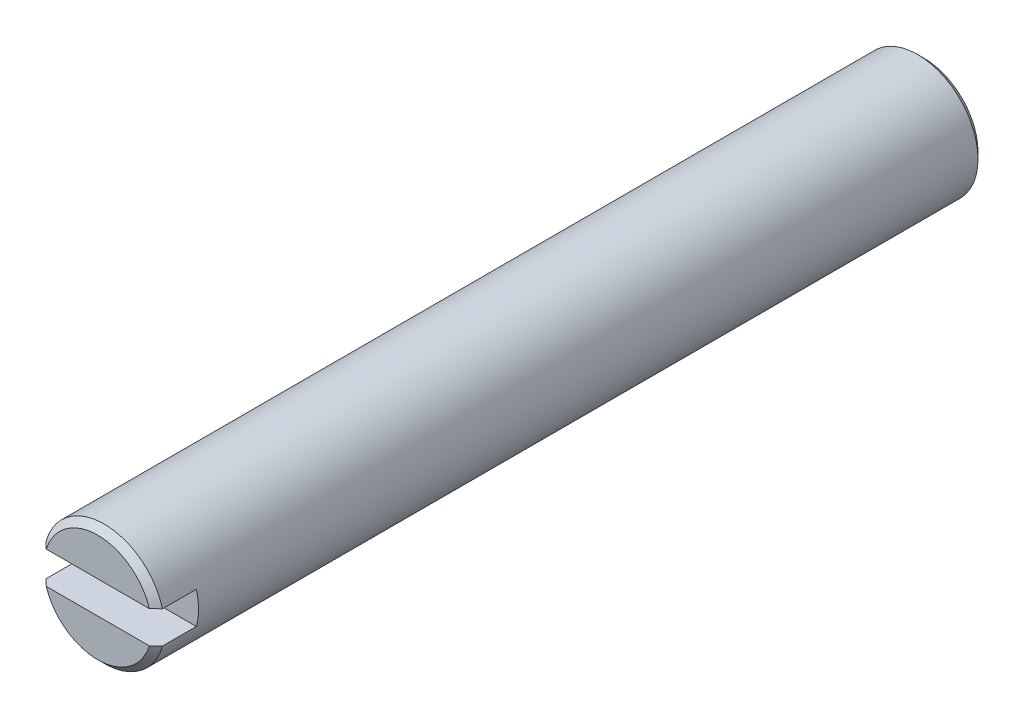
SolidWorks part; units mm, degrees
ref_plane "Front Plane" through (0, 0, 0) normal (0, 0, 1) x (1, 0, 0)
ref_plane "Top Plane" through (0, 0, 0) normal (0, 1, 0) x (1, 0, 0)
ref_plane "Right Plane" through (0, 0, 0) normal (1, 0, 0) x (0, 0, -1)
sketch "Sketch2" plane through (0, 0, 0) normal (0, 0, 1) x (1, 0, 0)
  circle A0 centre (0, 0) radius 4.7625
extrude "Boss-Extrude1" add sketch "Sketch2" along normal blind 65.1002
sketch "Sketch3" plane through (0, 0, 65.1002) normal (0, 0, 1) x (1, 0, 0)
  line L2 (4.7625, 0) -> (4.7625, 1.27)
  line L3 (4.7625, 1.27) -> (-4.7625, 1.27)
  line L4 (-4.7625, -1.27) -> (4.7625, -1.27)
  line L5 (4.7625, -1.27) -> (4.7625, 0)
  line L6 (-4.7625, -1.27) -> (-4.7625, 0)
  line L7 (-4.7625, 0) -> (-4.7625, 1.27)
  circle A1 centre (0, 0) radius 4.7625 construction
  point P4 (0, 0)
extrude "Cut-Extrude1" cut sketch "Sketch3" against normal blind 3.175
chamfer "Chamfer1" distance 0.508 angle 45 3 edges at (4.7625, 0, 0) (0, -4.7625, 65.1002) (0, 4.7625, 65.1002)
